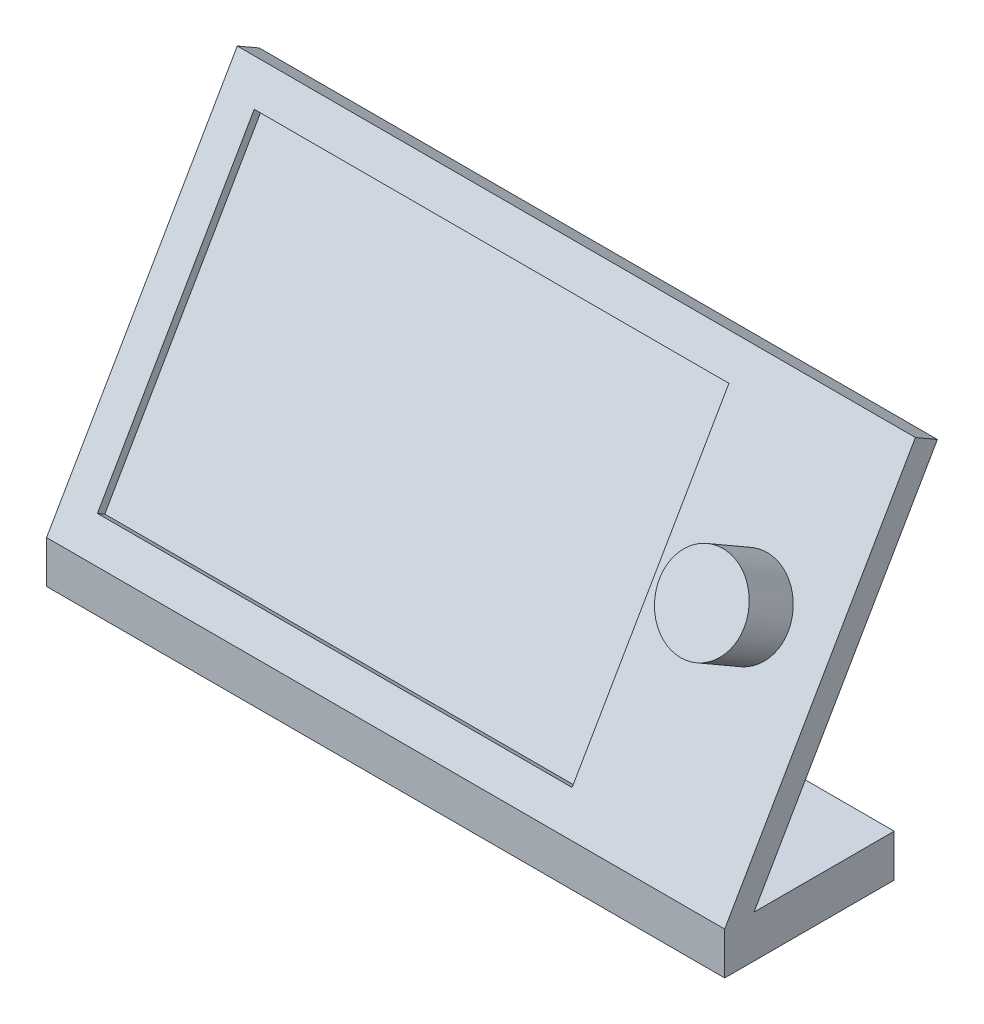
SolidWorks part; units mm, degrees
ref_plane "Front Plane" through (0, 0, 0) normal (0, 0, 1) x (1, 0, 0)
ref_plane "Top Plane" through (0, 0, 0) normal (0, 1, 0) x (1, 0, 0)
ref_plane "Right Plane" through (0, 0, 0) normal (1, 0, 0) x (0, 0, -1)
sketch "Sketch1" plane through (0, 0, 0) normal (0, 0, 1) x (1, 0, 0)
  line L1 (0, 0) -> (-101.6, 0)
  line L2 (0, 0) -> (0, 6.35)
  line L3 (0, 6.35) -> (-101.6, 6.35)
  line L4 (-101.6, 0) -> (-101.6, 6.35)
  dimension "D1" = 6.35
  dimension "D2" = 101.6
extrude "Boss-Extrude1" add sketch "Sketch1" along normal blind 25.4
sketch "Sketch2" plane through (0, 0, 0) normal (1, 0, 0) x (0, 0, -1)
  line L0 (-25.4, 6.35) -> (3.175, 55.8434)
  line L1 (-25.4, 6.35) -> (0, 6.35) construction
  line L2 (3.175, 55.8434) -> (6.4746, 53.9384)
  line L3 (6.4746, 53.9384) -> (-21.0006, 6.35)
  line L4 (-25.4, 6.35) -> (-21.0006, 6.35)
  dimension "D1" = 60
  dimension "D2" = 57.15
  dimension "D3" = 3.81
extrude "Boss-Extrude2" add sketch "Sketch2" against normal up to surface (101.6 mm away) up to face at (-101.6, 3.175, 12.7)
sketch "Sketch3" plane through (0, 12.586, 21.7996) normal (0, 0.5, 0.866) x (1, 0, 0)
  line L0 (-101.6, -7.2007) -> (-101.6, 49.9493) construction
  line L1 (-96.52, 44.8693) -> (-25.4, 44.8693)
  line L2 (-96.52, 44.8693) -> (-96.52, -2.1207)
  line L3 (-96.52, -2.1207) -> (-25.4, -2.1207)
  line L4 (-25.4, 44.8693) -> (-25.4, -2.1207)
  line L5 (-101.6, 49.9493) -> (0, 49.9493) construction
  line L6 (0, -7.2007) -> (-101.6, -7.2007) construction
  line L7 (0, 49.9493) -> (0, -7.2007) construction
  dimension "D1" = 5.08
  dimension "D2" = 5.08
  dimension "D3" = 5.08
  dimension "D4" = 25.4
extrude "Cut-Extrude1" cut sketch "Sketch3" against normal blind 1.27
sketch "Sketch4" plane through (0, 12.586, 21.7996) normal (0, 0.5, 0.866) x (1, 0, 0)
  line L0 (0, 49.9493) -> (0, -7.2007) construction
  line L2 (-101.6, 49.9493) -> (0, 49.9493) construction
  circle A0 centre (-12.7, 24.5493) radius 6.35
  dimension "D1" = 12.7
  dimension "D2" = 12.7
  dimension "D3" = 25.4
extrude "Boss-Extrude3" add sketch "Sketch4" along normal blind 7.62
